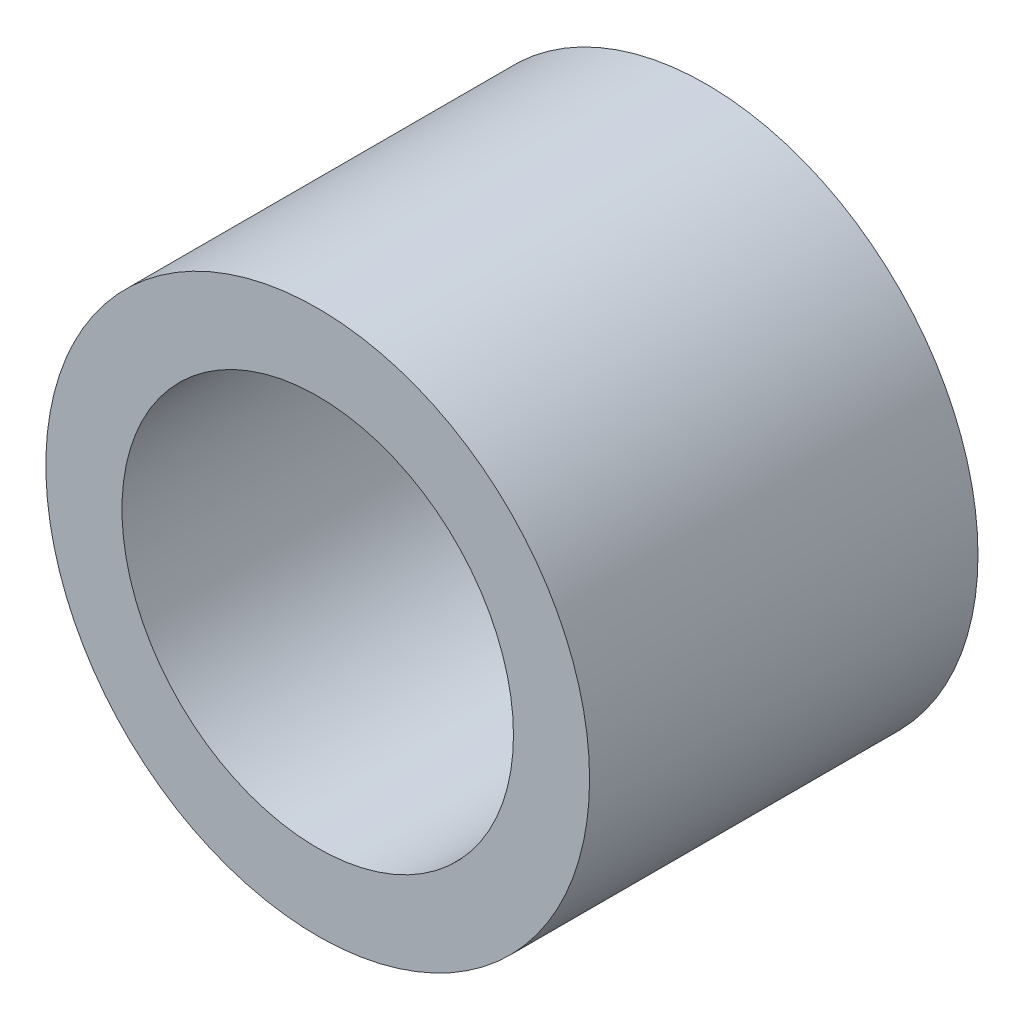
SolidWorks part; units mm, degrees
ref_plane "Front Plane" through (0, 0, 0) normal (0, 0, 1) x (1, 0, 0)
ref_plane "Top Plane" through (0, 0, 0) normal (0, 1, 0) x (1, 0, 0)
ref_plane "Right Plane" through (0, 0, 0) normal (1, 0, 0) x (0, 0, -1)
sketch "Sketch1" plane through (0, 0, 0) normal (0, 0, 1) x (1, 0, 0)
  circle A0 centre (0, 0) radius 11.1125
  circle A1 centre (0, 0) radius 8.001
  dimension "D1" = 22.225
  dimension "ID" = 16.002
extrude "Extrude1" add sketch "Sketch1" along normal mid plane 15.875
sketch "Sketch2" plane through (0, 0, 0) normal (1, 0, 0) x (0, 0, -1)
  line L0 (-7.9375, -8.001) -> (7.9375, -8.001) construction
  line L3 (7.9375, 8.001) -> (-7.9375, 8.001) construction
  line L5 (-7.9375, -8.001) -> (7.9375, -8.001)
  line L6 (7.9375, 8.001) -> (-7.9375, 8.001)
sketch "Sketch4" plane through (0, 0, 7.9375) normal (0, 0, 1) x (1, 0, 0)
  line L0 (0, 0) -> (-5.6576, 5.6576)
  line L1 (0, -6.985) -> (0, 6.985) construction
  circle A0 centre (0, 0) radius 8.001 construction
  dimension "D1" = 45
